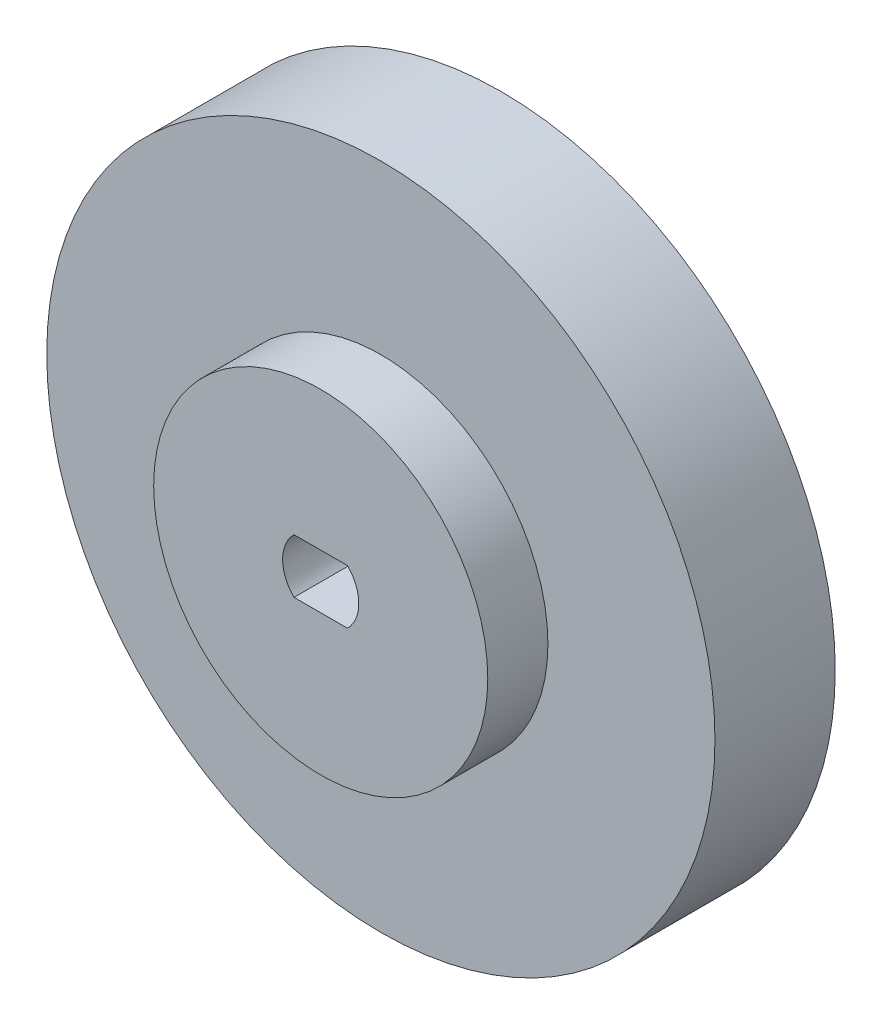
SolidWorks part; units mm, degrees
ref_plane "Front Plane" through (0, 0, 0) normal (0, 0, 1) x (1, 0, 0)
ref_plane "Top Plane" through (0, 0, 0) normal (0, 1, 0) x (1, 0, 0)
ref_plane "Right Plane" through (0, 0, 0) normal (1, 0, 0) x (0, 0, -1)
sketch "Sketch1" plane through (0, 0, 0) normal (0, 0, 1) x (1, 0, 0)
  line L0 (-34.1361, 0) -> (38.3541, 0) construction
  line L1 (0, 21.5067) -> (0, -21.6048) construction
  circle A0 centre (0, -0.049) radius 12.5
  dimension "D1" = 25
extrude "Boss-Extrude1" add sketch "Sketch1" along normal blind 18
sketch "Sketch2" plane through (0, 0, 18) normal (0, 0, 1) x (1, 0, 0)
  circle A0 centre (0, 0) radius 25
  dimension "D1" = 50
extrude "Boss-Extrude2" add sketch "Sketch2" against normal blind 9 from offset 4.5 offset against normal yes
sketch "Sketch3" plane through (0, 0, 18) normal (0, 0, 1) x (1, 0, 0)
  line L0 (-9.6925, 0) -> (15.432, 0) construction
  line L1 (-2, 2.0304) -> (2, 2.0304)
  line L2 (-2, -2.0304) -> (2, -2.0304)
  arc A0 (-2, 2.0304) -> (-2, -2.0304) centre (0, 0) ccw
  arc A1 (2, -2.0304) -> (2, 2.0304) centre (0, 0) ccw
  dimension "D1" = 5.7
  dimension "D2" = 4
extrude "Cut-Extrude1" cut sketch "Sketch3" against normal through all
